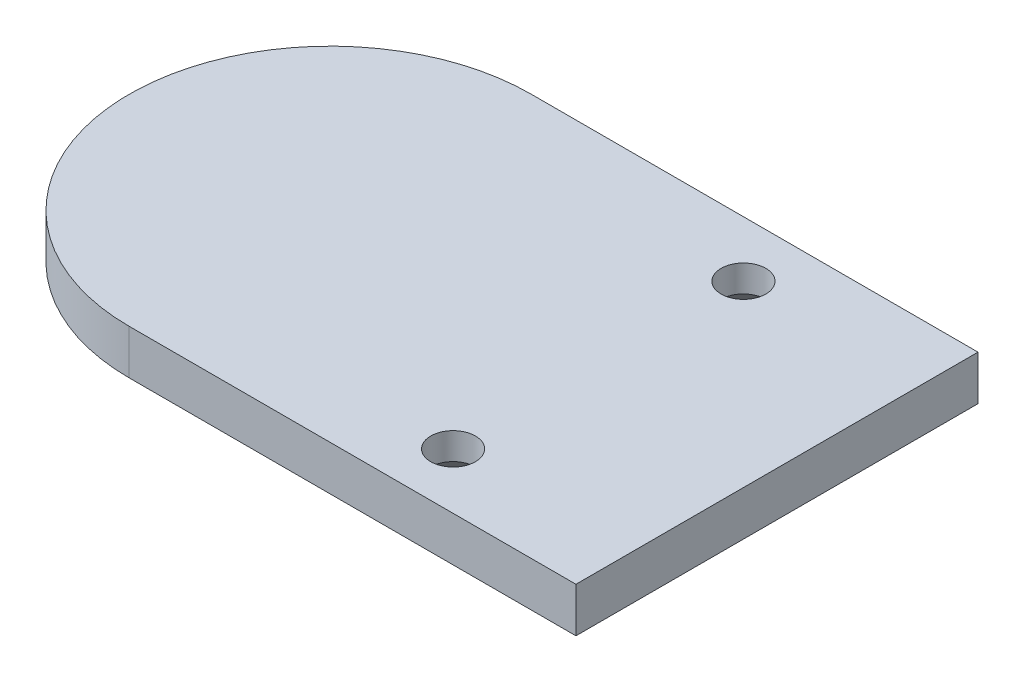
SolidWorks part; units mm, degrees
material "3003 Alloy"
ref_plane "Front Plane" through (0, 0, 0) normal (0, 0, 1) x (1, 0, 0)
ref_plane "Top Plane" through (0, 0, 0) normal (0, 1, 0) x (1, 0, 0)
ref_plane "Right Plane" through (0, 0, 0) normal (1, 0, 0) x (0, 0, -1)
sketch "Sketch1" plane through (0, 0, 0) normal (0, 1, 0) x (1, 0, 0)
  line L0 (0, 22.5) -> (50, 22.5)
  line L1 (50, 22.5) -> (50, -22.5)
  line L2 (50, -22.5) -> (0, -22.5)
  circle A0 centre (0, 0) radius 22.5 construction
  arc A1 (0, 22.5) -> (0, -22.5) centre (0, 0) ccw
  dimension "D1" = 45
  dimension "D2" = 50
extrude "Boss-Extrude1" add sketch "Sketch1" along normal blind 5
sketch "Sketch2" plane through (0, 0, 0) normal (0, 1, 0) x (1, 0, 0)
  line L0 (-6.3248, 25) -> (54.0535, 25) construction
  line L1 (50, 22.5) -> (0, 22.5) construction
  line L2 (-1.2682, 16.25) -> (52.191, 16.25) construction
  line L3 (-2.75, 0) -> (2.75, 0) construction
  line L4 (-1.2682, -16.25) -> (52.191, -16.25) construction
  line L5 (-6.3248, -25) -> (54.0535, -25) construction
  circle A0 centre (30, 16.25) radius 2.5
  circle A1 centre (30, -16.25) radius 2.5
  dimension "D1" = 5
  dimension "D2" = 2.5
  dimension "D3" = 8.75
  dimension "D4" = 30
extrude "Cut-Extrude1" cut sketch "Sketch2" along normal through all both and the other way through all
chamfer "Chamfer1" distance 2 angle 45 2 edges at (30, 0, -13.75) (30, 0, 18.75)
